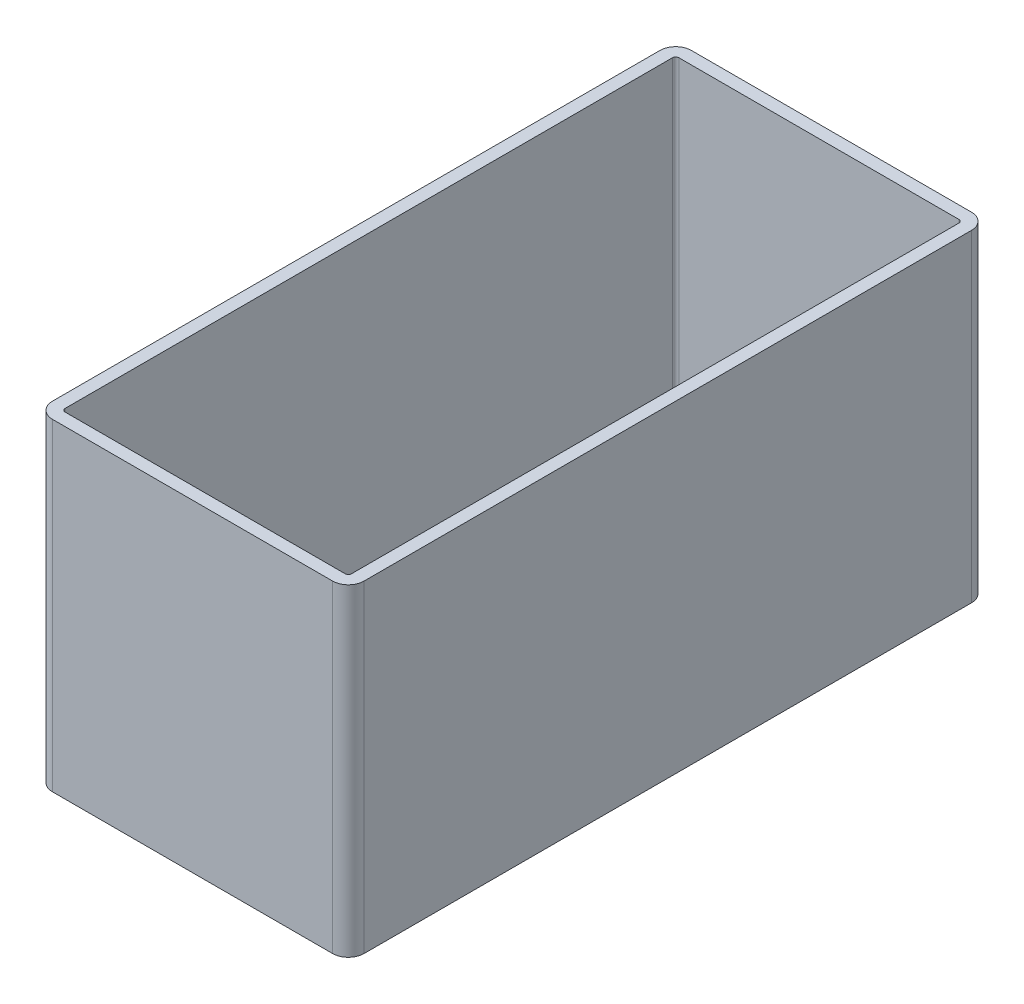
SolidWorks part; units mm, degrees
material "PC High Viscosity"
ref_plane "Front Plane" through (0, 0, 0) normal (0, 0, 1) x (1, 0, 0)
ref_plane "Top Plane" through (0, 0, 0) normal (0, 1, 0) x (1, 0, 0)
ref_plane "Right Plane" through (0, 0, 0) normal (1, 0, 0) x (0, 0, -1)
sketch "BaseS" plane through (0, 0, 0) normal (0, 1, 0) x (1, 0, 0)
  line L1 (-9.9, 20.3) -> (9.9, 20.3)
  line L2 (-9.9, 20.3) -> (-9.9, -20.3)
  line L3 (-9.9, -20.3) -> (9.9, -20.3)
  line L4 (9.9, 20.3) -> (9.9, -20.3)
  line L5 (-9.9, 20.3) -> (9.9, -20.3) construction
  line L6 (-9.9, -20.3) -> (9.9, 20.3) construction
  point P0 (0, 0)
  dimension "D1" = 19.8
  dimension "D2" = 40.6
extrude "BASE" add sketch "BaseS" along normal mid plane 20.5
fillet "BASE F" radius 1 4 edges at (-9.9, 0, -20.3) (9.9, 0, -20.3) (9.9, 0, 20.3) (-9.9, 0, 20.3)
sketch "PocketS" plane through (0, 10.25, 0) normal (0, 1, 0) x (1, 0, 0)
  line L0 (8.9, 19.5) -> (-8.9, 19.5)
  line L1 (-9.1, 19.3) -> (-9.1, -19.3)
  line L2 (-8.9, -19.5) -> (8.9, -19.5)
  line L3 (9.1, -19.3) -> (9.1, 19.3)
  line L4 (8.9, 20.3) -> (-8.9, 20.3)
  line L5 (-9.9, 19.3) -> (-9.9, -19.3)
  line L6 (-8.9, -20.3) -> (8.9, -20.3)
  line L7 (9.9, -19.3) -> (9.9, 19.3)
  line L8 (8.9, 20.3) -> (-8.9, 20.3) construction
  line L9 (-9.9, 19.3) -> (-9.9, -19.3) construction
  line L10 (-8.9, -20.3) -> (8.9, -20.3) construction
  line L11 (9.9, -19.3) -> (9.9, 19.3) construction
  arc A0 (-8.9, 19.5) -> (-9.1, 19.3) centre (-8.9, 19.3) ccw
  arc A1 (-9.1, -19.3) -> (-8.9, -19.5) centre (-8.9, -19.3) ccw
  arc A2 (8.9, -19.5) -> (9.1, -19.3) centre (8.9, -19.3) ccw
  arc A3 (9.1, 19.3) -> (8.9, 19.5) centre (8.9, 19.3) ccw
  arc A4 (-8.9, 20.3) -> (-9.9, 19.3) centre (-8.9, 19.3) ccw
  arc A5 (-9.9, -19.3) -> (-8.9, -20.3) centre (-8.9, -19.3) ccw
  arc A6 (8.9, -20.3) -> (9.9, -19.3) centre (8.9, -19.3) ccw
  arc A7 (9.9, 19.3) -> (8.9, 20.3) centre (8.9, 19.3) ccw
  arc A8 (-8.9, 20.3) -> (-9.9, 19.3) centre (-8.9, 19.3) ccw construction
  arc A9 (-9.9, -19.3) -> (-8.9, -20.3) centre (-8.9, -19.3) ccw construction
  arc A10 (8.9, -20.3) -> (9.9, -19.3) centre (8.9, -19.3) ccw construction
  arc A11 (9.9, 19.3) -> (8.9, 20.3) centre (8.9, 19.3) ccw construction
  dimension "D1" = 0
  dimension "D2" = 0.8
extrude "Cut-Extrude3" cut sketch "PocketS" against normal through all
